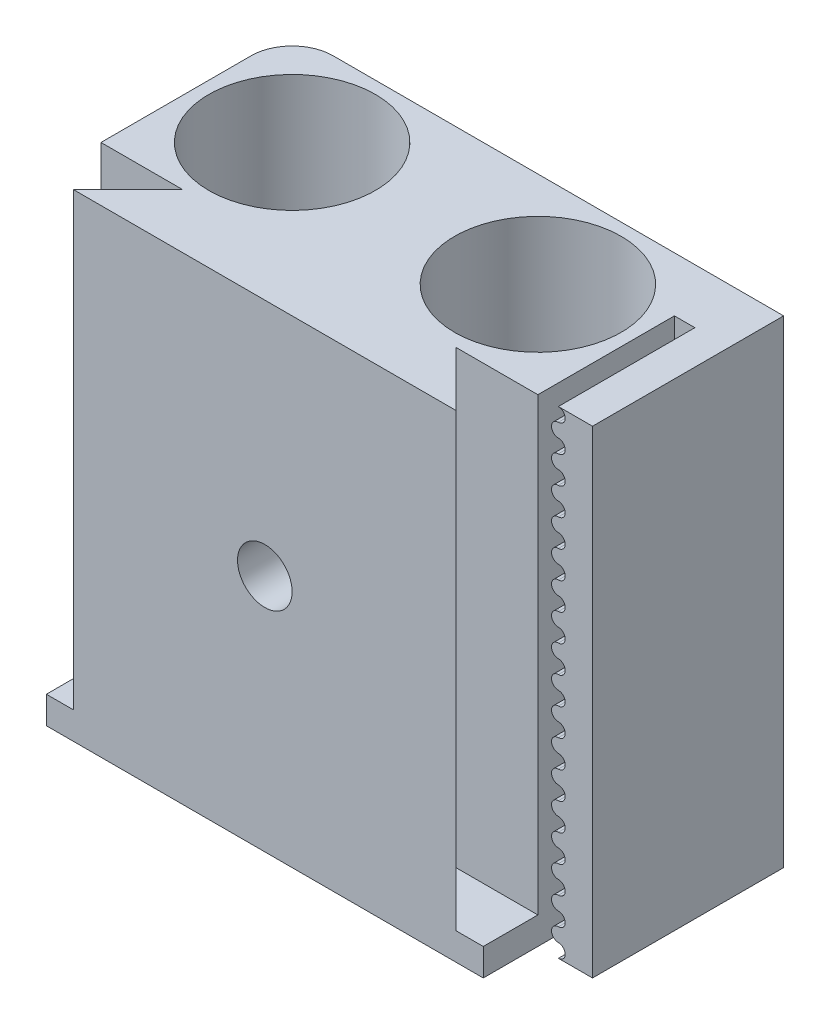
SolidWorks part; units mm, degrees
ref_plane "Спереди" through (0, 0, 0) normal (0, 0, 1) x (1, 0, 0)
ref_plane "Сверху" through (0, 0, 0) normal (0, 1, 0) x (1, 0, 0)
ref_plane "Справа" through (0, 0, 0) normal (1, 0, 0) x (0, 0, -1)
sketch "Эскиз1" plane through (0, 0, 0) normal (0, 0, 1) x (1, 0, 0)
  line L1 (-16, 17.5) -> (16, 17.5)
  line L2 (-16, 17.5) -> (-16, -17.5)
  line L3 (-16, -17.5) -> (16, -17.5)
  line L4 (16, 17.5) -> (16, -17.5)
  line L5 (-16, 17.5) -> (16, -17.5) construction
  line L6 (-16, -17.5) -> (16, 17.5) construction
  point P0 (0, 0)
  dimension "D1" = 32
  dimension "D2" = 35
extrude "Бобышка-Вытянуть1" add sketch "Эскиз1" along normal blind 14
sketch "Эскиз2" plane through (0, 17.5, 0) normal (0, 1, 0) x (1, 0, 0)
  line L0 (0, 0) -> (0, -14) construction
  line L1 (16, 0) -> (-16, 0) construction
  line L2 (16, -14) -> (-16, -14) construction
  circle A0 centre (-9, -7) radius 6.1
  circle A1 centre (9, -7) radius 6.1
  dimension "D1" = 9
extrude "Вырез-Вытянуть1" cut sketch "Эскиз2" against normal up to next
sketch "Эскиз3" plane through (0, 17.5, 0) normal (0, 1, 0) x (1, 0, 0)
  line L0 (-14, -18) -> (-10, -14)
  line L1 (-10, -14) -> (10, -14)
  line L3 (-14, -18) -> (14, -18)
  line L5 (14, -18) -> (10, -14)
  line L6 (0, 0) -> (0, -18) construction
  dimension "D1" = 4
  dimension "D2" = 45
  dimension "D3" = 45
  dimension "D4" = 28
extrude "Бобышка-Вытянуть2" add sketch "Эскиз3" against normal blind 33
sketch "Эскиз5" plane through (0, -15.5, 0) normal (0, -1, 0) x (1, 0, 0)
  line L1 (-16, 14) -> (16, 14)
  line L2 (-16, 14) -> (-16, 18)
  line L3 (-16, 18) -> (16, 18)
  line L4 (16, 14) -> (16, 18)
extrude "Бобышка-Вытянуть3" add sketch "Эскиз5" along normal blind 2
fillet "Скругление1" radius 3 1 edges at (-16, 0, 0)
sketch "Эскиз6" plane through (16, 0, 0) normal (1, 0, 0) x (0, 0, -1)
  line L0 (-18, -17.5) -> (0, -17.5) construction
  line L1 (0, 17.5) -> (-14, 17.5)
  line L2 (0, 17.5) -> (0, -17.5)
  line L3 (0, -17.5) -> (-14, -17.5)
  line L4 (-14, 17.5) -> (-14, -17.5)
extrude "Бобышка-Вытянуть4" add sketch "Эскиз6" along normal blind 4
sketch "Эскиз7" plane through (0, 0, 14) normal (0, 0, 1) x (1, 0, 0)
  line L0 (16, -17.5) -> (17.5, -17.5)
  line L2 (16, -17.5) -> (16, 17.5)
  line L3 (16, 17.5) -> (17.5, 17.5)
  line L5 (17.5, 17.5) -> (17.5, -17.5) construction
  arc A0 (17.5, 16.5) -> (17.5, 17.5) centre (17.5, 17) ccw
  arc A1 (17.5, 16.5) -> (17.5, 15.5) centre (17.5, 16) ccw
  arc A2 (17.5, 14.5) -> (17.5, 15.5) centre (17.5, 15) ccw
  arc A3 (17.5, 14.5) -> (17.5, 13.5) centre (17.5, 14) ccw
  arc A4 (17.5, 12.5) -> (17.5, 13.5) centre (17.5, 13) ccw
  arc A5 (17.5, 12.5) -> (17.5, 11.5) centre (17.5, 12) ccw
  arc A6 (17.5, 10.5) -> (17.5, 11.5) centre (17.5, 11) ccw
  arc A7 (17.5, 10.5) -> (17.5, 9.5) centre (17.5, 10) ccw
  arc A8 (17.5, 8.5) -> (17.5, 9.5) centre (17.5, 9) ccw
  arc A9 (17.5, 8.5) -> (17.5, 7.5) centre (17.5, 8) ccw
  arc A10 (17.5, 6.5) -> (17.5, 7.5) centre (17.5, 7) ccw
  arc A11 (17.5, 6.5) -> (17.5, 5.5) centre (17.5, 6) ccw
  arc A12 (17.5, 4.5) -> (17.5, 5.5) centre (17.5, 5) ccw
  arc A13 (17.5, 4.5) -> (17.5, 3.5) centre (17.5, 4) ccw
  arc A14 (17.5, 2.5) -> (17.5, 3.5) centre (17.5, 3) ccw
  arc A15 (17.5, 2.5) -> (17.5, 1.5) centre (17.5, 2) ccw
  arc A16 (17.5, 0.5) -> (17.5, 1.5) centre (17.5, 1) ccw
  arc A17 (17.5, 0.5) -> (17.5, -0.5) centre (17.5, 0) ccw
  arc A18 (17.5, -1.5) -> (17.5, -0.5) centre (17.5, -1) ccw
  arc A19 (17.5, -1.5) -> (17.5, -2.5) centre (17.5, -2) ccw
  arc A20 (17.5, -3.5) -> (17.5, -2.5) centre (17.5, -3) ccw
  arc A21 (17.5, -3.5) -> (17.5, -4.5) centre (17.5, -4) ccw
  arc A22 (17.5, -5.5) -> (17.5, -4.5) centre (17.5, -5) ccw
  arc A23 (17.5, -5.5) -> (17.5, -6.5) centre (17.5, -6) ccw
  arc A24 (17.5, -7.5) -> (17.5, -6.5) centre (17.5, -7) ccw
  arc A25 (17.5, -7.5) -> (17.5, -8.5) centre (17.5, -8) ccw
  arc A26 (17.5, -9.5) -> (17.5, -8.5) centre (17.5, -9) ccw
  arc A27 (17.5, -9.5) -> (17.5, -10.5) centre (17.5, -10) ccw
  arc A28 (17.5, -11.5) -> (17.5, -10.5) centre (17.5, -11) ccw
  arc A29 (17.5, -11.5) -> (17.5, -12.5) centre (17.5, -12) ccw
  arc A30 (17.5, -13.5) -> (17.5, -12.5) centre (17.5, -13) ccw
  arc A31 (17.5, -13.5) -> (17.5, -14.5) centre (17.5, -14) ccw
  arc A32 (17.5, -15.5) -> (17.5, -14.5) centre (17.5, -15) ccw
  arc A33 (17.5, -15.5) -> (17.5, -16.5) centre (17.5, -16) ccw
  arc A34 (17.5, -17.5) -> (17.5, -16.5) centre (17.5, -17) ccw
  arc A36 (17.5, -17.5) -> (17.5, -18.5) centre (17.5, -18) ccw [skipped]
  dimension "D2" = 0.5
  dimension "D1" = 1.5
  dimension "D3" = 18
extrude "Вырез-Вытянуть2" cut sketch "Эскиз7" against normal blind 10
sketch "Эскиз9" plane through (0, 0, 18) normal (0, 0, 1) x (1, 0, 0)
  circle A0 centre (0, 0) radius 2
extrude "Вырез-Вытянуть3" cut sketch "Эскиз9" against normal up to next
sketch "Эскиз10" plane through (0, 0, 0) normal (0, 0, -1) x (-1, 0, 0)
  line L1 (0, -4.0415) -> (3.5, -2.0207)
  line L2 (3.5, -2.0207) -> (3.5, 2.0207)
  line L3 (3.5, 2.0207) -> (0, 4.0415)
  line L4 (0, 4.0415) -> (-3.5, 2.0207)
  line L5 (-3.5, 2.0207) -> (-3.5, -2.0207)
  line L6 (-3.5, -2.0207) -> (0, -4.0415)
  circle A0 centre (0, 0) radius 3.5 construction
extrude "Вырез-Вытянуть4" cut sketch "Эскиз10" against normal blind 3.5
